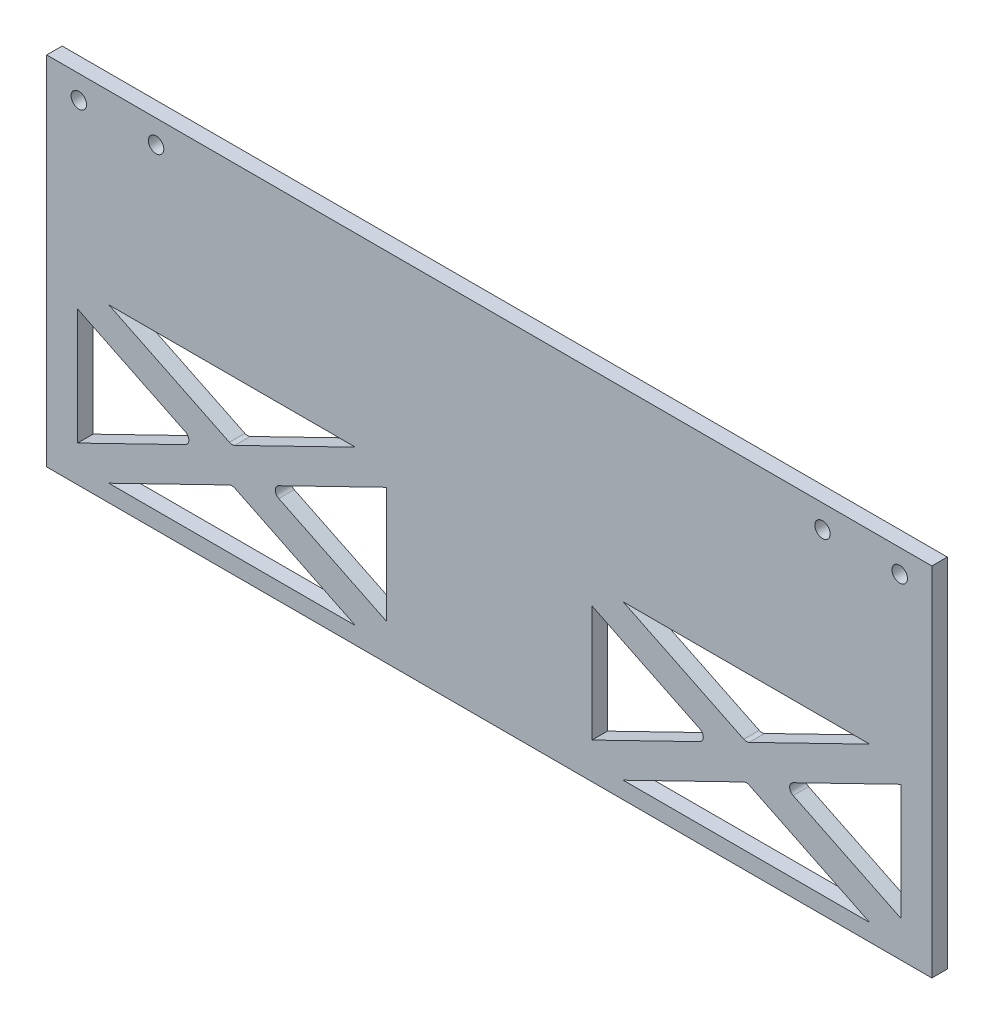
SolidWorks part; units mm, degrees
material "Acrylic (Medium-high impact)"
ref_plane "Front Plane" through (0, 0, 0) normal (0, 0, 1) x (1, 0, 0)
ref_plane "Top Plane" through (0, 0, 0) normal (0, 1, 0) x (1, 0, 0)
ref_plane "Right Plane" through (0, 0, 0) normal (1, 0, 0) x (0, 0, -1)
sketch "Sketch6" plane through (0, 0, 0) normal (0, 0, 1) x (1, 0, 0)
  line L0 (-143.25, 0) -> (143.25, 0)
  line L1 (-143.25, 180) -> (143.25, 180)
  line L2 (-143.25, 180) -> (-143.25, 0)
  line L4 (143.25, 180) -> (143.25, 0)
  line L5 (-143.25, 180) -> (0, 0) construction
  line L6 (0, 0) -> (143.25, 180) construction
  line L7 (0, 0) -> (0, -41.3687) construction
  point P0 (0, 0)
  dimension "D1" = 286.5
  dimension "D2" = 180
extrude "Boss-Extrude3" add sketch "Sketch6" along normal blind 5
sketch "Sketch7" plane through (0, 0, 5) normal (0, 0, 1) x (1, 0, 0)
  line L0 (143.25, 0) -> (143.25, 180) construction
  line L1 (-143.25, 180) -> (-143.25, 0) construction
  line L2 (143.25, 180) -> (-143.25, 180) construction
  line L3 (-143.25, 0) -> (143.25, 0) construction
  line L4 (-133.25, 60) -> (-33.25, 60)
  line L5 (-133.25, 60) -> (-133.25, 10)
  line L6 (-133.25, 10) -> (-33.25, 10)
  line L7 (-33.25, 60) -> (-33.25, 10)
  line L8 (-133.25, 16.2024) -> (-98.3566, 33.202)
  line L9 (-123.1487, 10) -> (-84.126, 29.0114)
  line L10 (-83.25, 60) -> (-83.25, 10) construction
  line L11 (-43.3513, 10) -> (-82.374, 29.0114)
  line L12 (-33.25, 16.2024) -> (-68.1434, 33.202)
  line L13 (-143.25, 65) -> (143.25, 65) construction
  line L14 (-98.3566, 36.798) -> (-133.25, 53.7976)
  line L15 (-84.126, 40.9886) -> (-123.1487, 60)
  line L16 (-68.1434, 36.798) -> (-33.25, 53.7976)
  line L17 (-82.374, 40.9886) -> (-43.3513, 60)
  line L18 (-83.25, 70) -> (-83.25, 120) construction
  line L19 (-82.374, 89.0114) -> (-43.3513, 70)
  line L20 (-68.1434, 93.202) -> (-33.25, 76.2024)
  line L21 (-84.126, 89.0114) -> (-123.1487, 70)
  line L22 (-98.3566, 93.202) -> (-133.25, 76.2024)
  line L23 (-33.25, 113.7976) -> (-68.1434, 96.798)
  line L24 (-43.3513, 120) -> (-82.374, 100.9886)
  line L25 (-123.1487, 120) -> (-84.126, 100.9886)
  line L26 (-133.25, 113.7976) -> (-98.3566, 96.798)
  line L27 (-33.25, 70) -> (-33.25, 120)
  line L28 (-133.25, 120) -> (-33.25, 120)
  line L29 (-133.25, 70) -> (-133.25, 120)
  line L30 (-133.25, 70) -> (-33.25, 70)
  line L31 (0, 180) -> (0, 0) construction
  line L32 (83.25, 70) -> (83.25, 120) construction
  line L33 (83.25, 60) -> (83.25, 10) construction
  line L34 (133.25, 70) -> (33.25, 70)
  line L35 (133.25, 70) -> (133.25, 120)
  line L36 (133.25, 120) -> (33.25, 120)
  line L37 (33.25, 70) -> (33.25, 120)
  line L38 (133.25, 113.7976) -> (98.3566, 96.798)
  line L39 (123.1487, 120) -> (84.126, 100.9886)
  line L40 (43.3513, 120) -> (82.374, 100.9886)
  line L41 (33.25, 113.7976) -> (68.1434, 96.798)
  line L42 (98.3566, 93.202) -> (133.25, 76.2024)
  line L43 (84.126, 89.0114) -> (123.1487, 70)
  line L44 (68.1434, 93.202) -> (33.25, 76.2024)
  line L45 (82.374, 89.0114) -> (43.3513, 70)
  line L46 (82.374, 40.9886) -> (43.3513, 60)
  line L47 (68.1434, 36.798) -> (33.25, 53.7976)
  line L48 (84.126, 40.9886) -> (123.1487, 60)
  line L49 (98.3566, 36.798) -> (133.25, 53.7976)
  line L50 (33.25, 16.2024) -> (68.1434, 33.202)
  line L51 (43.3513, 10) -> (82.374, 29.0114)
  line L52 (123.1487, 10) -> (84.126, 29.0114)
  line L53 (133.25, 16.2024) -> (98.3566, 33.202)
  line L54 (33.25, 60) -> (33.25, 10)
  line L55 (133.25, 10) -> (33.25, 10)
  line L56 (133.25, 60) -> (133.25, 10)
  line L57 (133.25, 60) -> (33.25, 60)
  circle A0 centre (132.85, 172.5) radius 2.5
  circle A1 centre (107.85, 172.5) radius 2.5
  circle A2 centre (-132.85, 172.5) radius 2.5
  circle A3 centre (-107.85, 172.5) radius 2.5
  arc A4 (-82.374, 29.0114) -> (-84.126, 29.0114) centre (-83.25, 27.2135) ccw
  arc A5 (-68.1434, 33.202) -> (-68.1434, 36.798) centre (-67.2674, 35) cw
  arc A6 (-82.374, 40.9886) -> (-84.126, 40.9886) centre (-83.25, 42.7865) cw
  arc A7 (-98.3566, 33.202) -> (-98.3566, 36.798) centre (-99.2326, 35) ccw
  arc A8 (-98.3566, 96.798) -> (-98.3566, 93.202) centre (-99.2326, 95) cw
  arc A9 (-82.374, 89.0114) -> (-84.126, 89.0114) centre (-83.25, 87.2135) ccw
  arc A10 (-68.1434, 96.798) -> (-68.1434, 93.202) centre (-67.2674, 95) ccw
  arc A11 (-82.374, 100.9886) -> (-84.126, 100.9886) centre (-83.25, 102.7865) cw
  arc A12 (82.374, 100.9886) -> (84.126, 100.9886) centre (83.25, 102.7865) ccw
  arc A13 (68.1434, 96.798) -> (68.1434, 93.202) centre (67.2674, 95) cw
  arc A14 (82.374, 89.0114) -> (84.126, 89.0114) centre (83.25, 87.2135) cw
  arc A15 (98.3566, 96.798) -> (98.3566, 93.202) centre (99.2326, 95) ccw
  arc A16 (98.3566, 33.202) -> (98.3566, 36.798) centre (99.2326, 35) cw
  arc A17 (82.374, 40.9886) -> (84.126, 40.9886) centre (83.25, 42.7865) ccw
  arc A18 (68.1434, 33.202) -> (68.1434, 36.798) centre (67.2674, 35) ccw
  arc A19 (82.374, 29.0114) -> (84.126, 29.0114) centre (83.25, 27.2135) cw
  point P38 (-83.25, 29.4382)
  point P41 (-71.8339, 35)
  point P44 (-83.25, 40.5618)
  point P47 (-94.6661, 35)
  point P74 (-94.6661, 95)
  point P75 (-83.25, 89.4382)
  point P76 (-71.8339, 95)
  point P77 (-83.25, 100.5618)
  point P133 (83.25, 100.5618)
  point P134 (71.8339, 95)
  point P135 (83.25, 89.4382)
  point P136 (94.6661, 95)
  point P137 (94.6661, 35)
  point P138 (83.25, 40.5618)
  point P139 (71.8339, 35)
  point P140 (83.25, 29.4382)
  dimension "D1" = 5
  dimension "D3" = 25
  dimension "D4" = 10.4
  dimension "D9" = 5
  dimension "D10" = 5
  dimension "D11" = 5
  dimension "D21" = 2
  dimension "D2" = 10.4
  dimension "D5" = 25
  dimension "D6" = 7.5
  dimension "D7" = 7.5
  dimension "D8" = 7.5
  dimension "D12" = 7.5
  dimension "D13" = 100
  dimension "D14" = 50
  dimension "D15" = 10
  dimension "D16" = 10
  dimension "D17" = 10
  dimension "D18" = 100
  dimension "D19" = 5
  dimension "D20" = 25
extrude "Cut-Extrude1" cut sketch "Sketch7" against normal blind 13 contours A2 | A3 | A11 L24 L28 L25 | A8 L26 L29 L22 | L23 A10 L20 L27 | L19 A9 L21 L30 | A6 L17 L4 L15 | L8 A7 L14 L5 | A5 L12 L7 L16 | L11 A4 L9 L6 | L40 A12 L39 L36 | A13 L41 L37 L44 | L38 A15 L42 L35 | A14 L45 L34 L43 | L46 A17 L48 L57 | L50 A18 L47 L54 | A16 L53 L56 L49 | A19 L51 L55 L52 | A1 | A0
sketch "Sketch8" plane through (0, 0, 5) normal (0, 0, 1) x (1, 0, 0)
  line L0 (-143.25, 180) -> (-143.25, 0) construction
  line L1 (-143.25, 64.5) -> (143.25, 64.5)
  line L2 (-143.25, 64.5) -> (-143.25, 0)
  line L3 (-143.25, 0) -> (143.25, 0)
  line L4 (143.25, 64.5) -> (143.25, 0)
  dimension "D1" = 64.5
extrude "Cut-Extrude2" cut sketch "Sketch8" against normal through all
